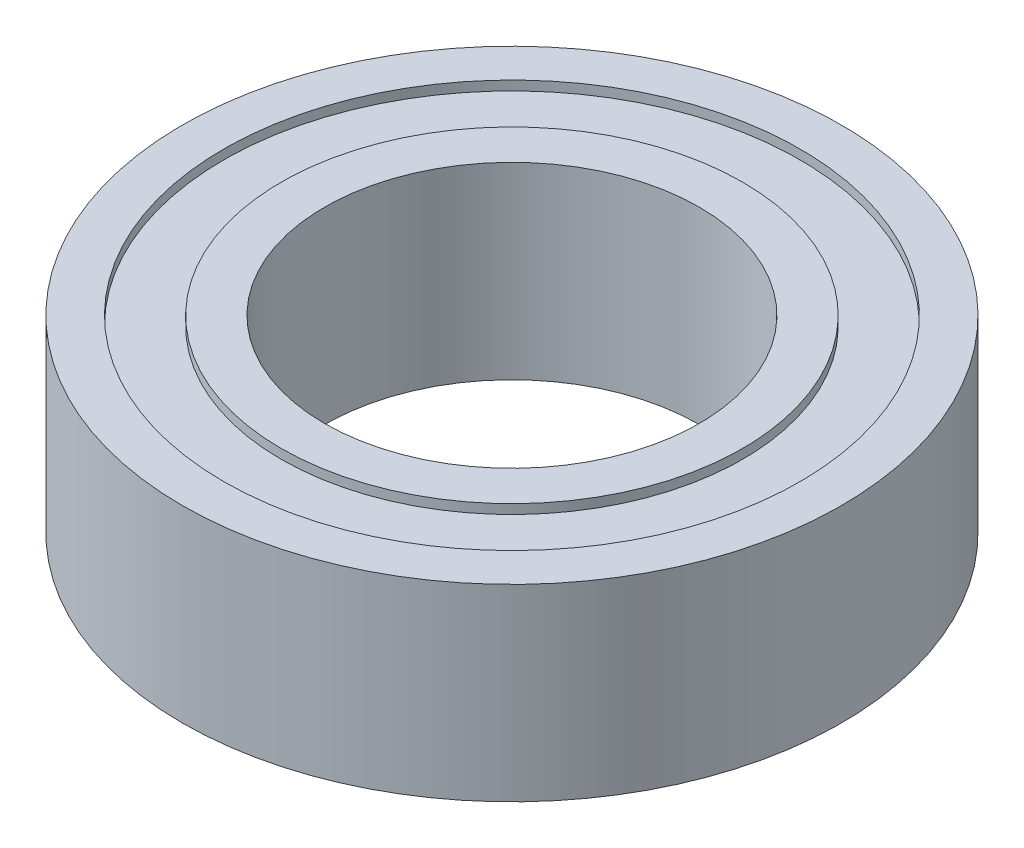
SolidWorks part; units mm, degrees
ref_plane "Front Plane" through (0, 0, 0) normal (0, 0, 1) x (1, 0, 0)
ref_plane "Top Plane" through (0, 0, 0) normal (0, 1, 0) x (1, 0, 0)
ref_plane "Right Plane" through (0, 0, 0) normal (1, 0, 0) x (0, 0, -1)
sketch "Sketch1" plane through (0, 0, 0) normal (0, 1, 0) x (1, 0, 0)
  circle A0 centre (0, 0) radius 7
  dimension "D1" = 14
extrude "Boss-Extrude1" add sketch "Sketch1" along normal mid plane 4
sketch "Sketch2" plane through (0, 0, 0) normal (0, 1, 0) x (1, 0, 0)
  circle A0 centre (0, 0) radius 3.98
  dimension "D1" = 7.96
extrude "Cut-Extrude1" cut sketch "Sketch2" against normal through all both and the other way through all
sketch "Sketch3" plane through (0, 0, 0) normal (0, 1, 0) x (1, 0, 0)
  circle A0 centre (0, 0) radius 4.9
  circle A1 centre (0, 0) radius 6.12
  circle A2 centre (0, 0) radius 7 construction
  dimension "D1" = 1.22
  dimension "D2" = 0.88
extrude "Cut-Extrude2" cut sketch "Sketch3" against normal blind 0.2 from surface at 2 starting at face at (0, 2, 3.98)
mirror "Mirror1" about plane through (0, 0, 0) normal (0, 1, 0) of "Cut-Extrude2"
